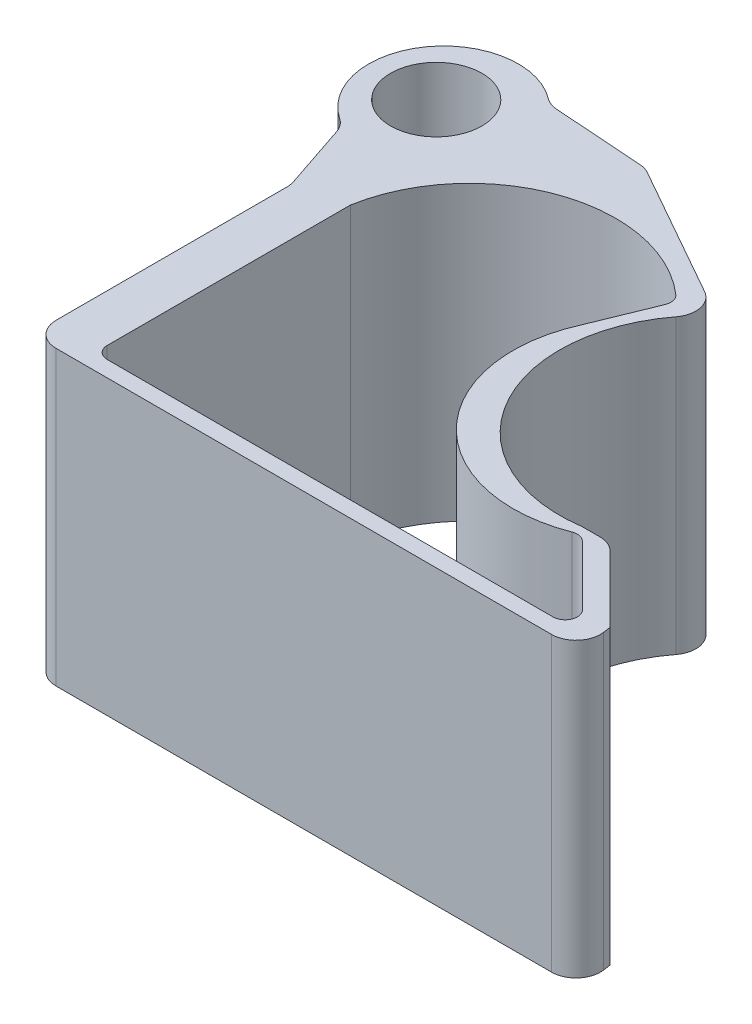
SolidWorks part; units mm, degrees
material "Markforged"
ref_plane "Front Plane" through (0, 0, 0) normal (0, 0, 1) x (1, 0, 0)
ref_plane "Top Plane" through (0, 0, 0) normal (0, 1, 0) x (1, 0, 0)
ref_plane "Right Plane" through (0, 0, 0) normal (1, 0, 0) x (0, 0, -1)
sketch "Sketch1" plane through (0, 0, 0) normal (0, 1, 0) x (1, 0, 0)
  line L0 (35.7754, 8.3677) -> (41.9881, 2.169)
  line L1 (41.0911, 0) -> (-5.3679, 0)
  line L2 (-6.6379, 1.27) -> (-6.6379, 26.6076)
  line L3 (16.2027, 27.8014) -> (18.7462, 34.0462)
  line L4 (5.3779, 45.3101) -> (22.4512, 35.6651)
  line L5 (5.3779, 45.3101) -> (-5.3679, 46.0642)
  line L6 (-14.2804, 33.4227) -> (-11.5757, 25.3612)
  line L7 (-11.5757, -1.6566) -> (45.5152, -1.6566)
  line L8 (45.0059, 2.0277) -> (37.3679, 9.6657)
  line L9 (-11.5757, 25.3612) -> (-11.5757, -1.6566)
  arc A0 (-6.6379, 26.6076) -> (18.4057, 35.4816) centre (8.3782, 24.0052) cw
  arc A1 (18.4057, 35.4816) -> (18.7462, 34.0462) centre (17.5701, 34.5253) cw
  arc A2 (-6.6379, 1.27) -> (-5.3679, 0) centre (-5.3679, 1.27) ccw
  arc A3 (41.9881, 2.169) -> (41.0911, 0) centre (41.0911, 1.27) cw
  arc A4 (34.4186, 8.6526) -> (35.7754, 8.3677) centre (34.8784, 7.4687) cw
  arc A5 (16.2027, 27.8014) -> (34.4186, 8.6526) centre (29.2464, 21.971) ccw
  circle A6 centre (-11.6788, 40.5984) radius 4.7625
  arc A7 (-14.2804, 33.4227) -> (-5.3679, 46.0642) centre (-10.6285, 40.3105) cw
  arc A8 (22.4512, 35.6651) -> (34.4325, 9.6657) centre (32.2505, 24.4206) ccw
  line B0 (22.4512, 35.6651) -> (5.3779, 45.3101)
  line B1 (34.4325, 9.6657) -> (37.3679, 9.6657)
  line B2 (37.3679, 9.6657) -> (45.0059, 2.0277)
  line B3 (45.0059, 2.0277) -> (45.5152, -1.6566)
  line B4 (45.5152, -1.6566) -> (-11.5757, -1.6566)
  line B5 (-11.5757, -1.6566) -> (-11.5757, 25.3612)
  line B6 (16.2027, 27.8014) -> (18.7462, 34.0462)
  line B7 (-6.6379, 26.6076) -> (-6.6379, 1.27)
  line B8 (-5.3679, 0) -> (41.0911, 0)
  line B9 (-11.5757, 25.3612) -> (-14.2804, 33.4227)
  line B10 (5.3779, 45.3101) -> (-5.3679, 46.0642)
  arc B11 (22.4512, 35.6651) -> (34.4325, 9.6657) centre (32.2505, 24.4206) ccw
  circle B12 centre (-11.6788, 40.5984) radius 4.7625
  arc B13 (18.7462, 34.0462) -> (18.4057, 35.4816) centre (17.5701, 34.5253) ccw
  arc B14 (18.4057, 35.4816) -> (-6.6379, 26.6076) centre (8.3782, 24.0052) ccw
  arc B15 (-6.6379, 1.27) -> (-5.3679, 0) centre (-5.3679, 1.27) ccw
  arc B16 (41.0911, 0) -> (41.9881, 2.169) centre (41.0911, 1.27) ccw
  arc B17 (34.4186, 8.6526) -> (35.7754, 8.3677) centre (34.8784, 7.4687) cw
  arc B18 (16.2027, 27.8014) -> (34.4186, 8.6526) centre (29.2464, 21.971) ccw
  arc B19 (-14.2804, 33.4227) -> (-5.3679, 46.0642) centre (-10.6285, 40.3105) cw
sketch_block_instance "Helper for Uprights-1"
sketch_block "Helper for Uprights"
extrude "Boss-Extrude2" add sketch "Sketch1" along normal blind 30.48 contours B3 L8 B1 A8 L4 L5 A7 L6 L9 L7 A6 L3 A5 A4 L0 A3 L1 A2 L2 A0 A1
fillet "Fillet1" radius 2.54 8 edges at (5.3779, 15.24, -45.3101) (-5.3679, 15.24, -46.0642) (-14.2804, 15.24, -33.4227) (-11.5757, 15.24, -25.3612) (-11.5757, 15.24, 1.6566) (45.5152, 15.24, 1.6566) (37.3679, 15.24, -9.6657) (22.4512, 15.24, -35.6651)
